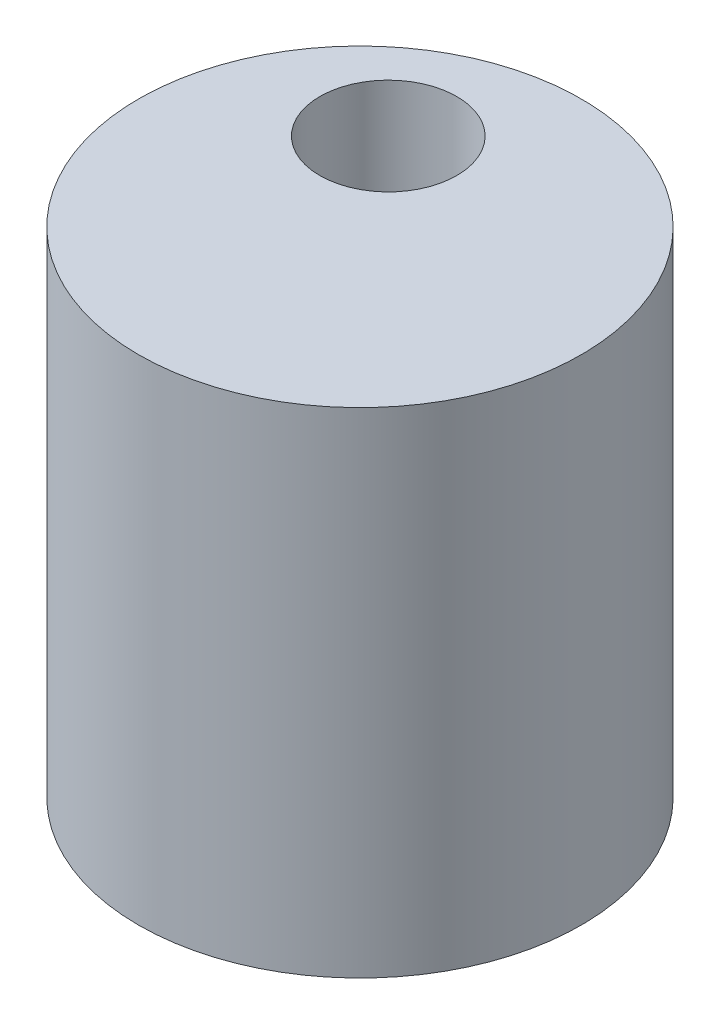
SolidWorks part; units mm, degrees
material "ABS PC"
ref_plane "X-Y Datum" through (0, 0, 0) normal (0, 0, 1) x (1, 0, 0)
ref_plane "X-Z Datum" through (0, 0, 0) normal (0, 1, 0) x (1, 0, 0)
ref_plane "Y-Z Datum" through (0, 0, 0) normal (1, 0, 0) x (0, 0, -1)
sketch "Sketch1" plane through (0, 0, 0) normal (0, 1, 0) x (1, 0, 0)
  line L0 (0, 0) -> (0, 5.4864) construction
  line L1 (0, 5.4864) -> (-3.81, 5.4864) construction
  circle A1 centre (0, 0) radius 13.0937
  circle A4 centre (-3.81, 5.4864) radius 4.05
  dimension "D1" = 26.1874
  dimension "D2" = 3.81
  dimension "D4" = 8.1
  dimension "D3" = 5.4864
extrude "Boss-Extrude1" add sketch "Sketch1" against normal blind 29.21
